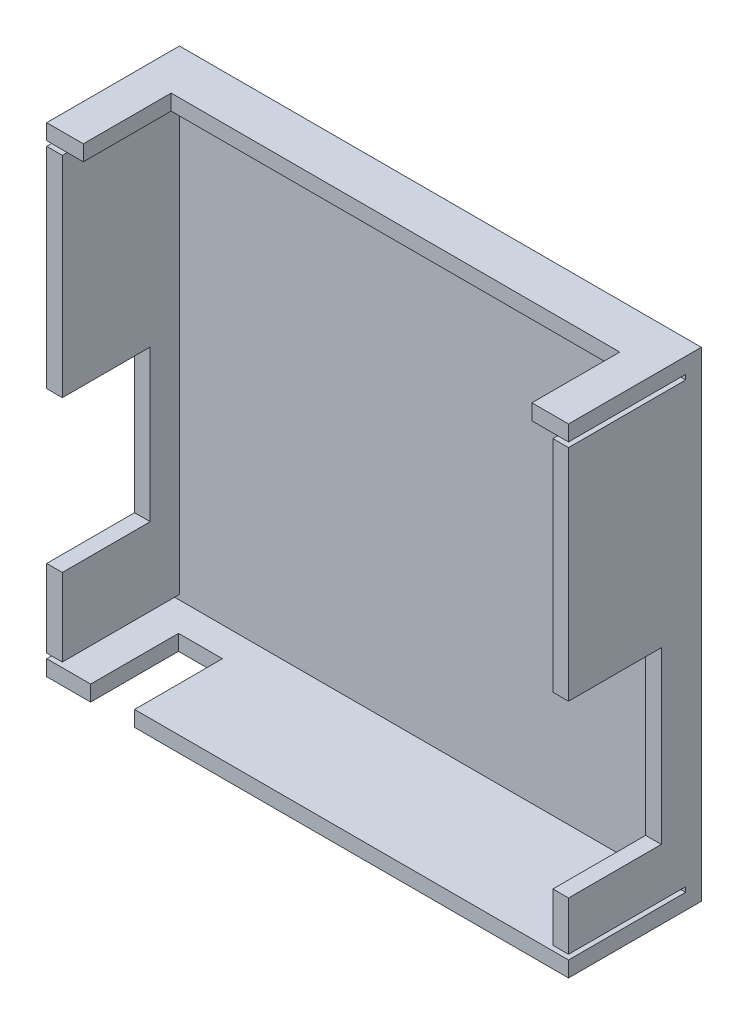
SolidWorks part; units mm, degrees
ref_plane "Front Plane" through (0, 0, 0) normal (0, 0, 1) x (1, 0, 0)
ref_plane "Top Plane" through (0, 0, 0) normal (0, 1, 0) x (1, 0, 0)
ref_plane "Right Plane" through (0, 0, 0) normal (1, 0, 0) x (0, 0, -1)
sketch "Sketch1" plane through (0, 0, 0) normal (0, 0, 1) x (1, 0, 0)
  line L1 (0, 0) -> (106.9, 0)
  line L2 (0, 0) -> (0, 98.3)
  line L3 (0, 98.3) -> (106.9, 98.3)
  line L4 (106.9, 0) -> (106.9, 98.3)
  dimension "D1" = 98.3
  dimension "D2" = 106.9
extrude "Boss-Extrude2" add sketch "Sketch1" along normal blind 3.2
sketch "Sketch2" plane through (0, 0, 3.2) normal (0, 0, 1) x (1, 0, 0)
  line L1 (3.2, 3.2) -> (103.7, 3.2)
  line L2 (3.2, 3.2) -> (3.2, 95.1)
  line L3 (3.2, 95.1) -> (103.7, 95.1)
  line L4 (0, 98.3) -> (0, 0)
  line L5 (0, 0) -> (106.9, 0)
  line L6 (106.9, 0) -> (106.9, 98.3)
  line L7 (106.9, 98.3) -> (0, 98.3)
  line L8 (0, 98.3) -> (0, 0)
  line L9 (0, 0) -> (106.9, 0)
  line L10 (106.9, 0) -> (106.9, 98.3)
  line L11 (106.9, 98.3) -> (0, 98.3)
  line L12 (103.7, 3.2) -> (103.7, 95.1)
  dimension "D2" = 3.2
  dimension "D3" = 3.2
  dimension "D4" = 3.2
  dimension "D5" = 3.2
  dimension "D1" = 0
extrude "Boss-Extrude3" add sketch "Sketch2" along normal blind 24
sketch "Sketch3" plane through (0, 0, 27.2) normal (0, 0, 1) x (1, 0, 0)
  line L0 (3.2, 95.1) -> (0, 95.1)
  line L1 (0, 95.1) -> (0, 94.1)
  line L2 (0, 94.1) -> (3.2, 94.1)
  line L3 (3.2, 95.1) -> (3.2, 3.2) construction
  line L4 (106.9, 98.3) -> (0, 98.3)
  line L5 (0, 98.3) -> (0, 0)
  line L6 (0, 0) -> (106.9, 0)
  line L7 (106.9, 0) -> (106.9, 98.3)
  line L9 (0, 95.1) -> (0, 94.1)
  line L11 (106.9, 3.2) -> (106.9, 4.2)
  line L12 (3.2, 94.1) -> (3.2, 95.1)
  line L13 (103.7, 95.1) -> (106.9, 95.1)
  line L14 (106.9, 95.1) -> (106.9, 94.1)
  line L15 (106.9, 94.1) -> (103.7, 94.1)
  line L16 (103.7, 3.2) -> (103.7, 95.1) construction
  line L17 (103.7, 94.1) -> (103.7, 95.1)
  line L18 (103.7, 3.2) -> (106.9, 3.2)
  line L19 (106.9, 3.2) -> (106.9, 4.2)
  line L20 (106.9, 4.2) -> (103.7, 4.2)
  line L21 (103.7, 4.2) -> (103.7, 3.2)
  line L22 (3.2, 3.2) -> (0, 3.2)
  line L23 (0, 3.2) -> (0, 4.2)
  line L24 (0, 4.2) -> (3.2, 4.2)
  line L25 (3.2, 4.2) -> (3.2, 3.2)
  line L26 (0, 4.2) -> (0, 0)
  line L27 (106.9, 94.1) -> (106.9, 95.1)
  line M10 (0, 98.3) -> (0, 0)
  line M12 (106.9, 0) -> (106.9, 98.3)
  line M14 (3.2, 3.2) -> (3.2, 95.1)
  line M16 (103.7, 95.1) -> (103.7, 3.2)
  dimension "D1" = 0
  dimension "D2" = 1
  dimension "D3" = 1
  dimension "D4" = 1
  dimension "D5" = 1
extrude "Cut-Extrude1" cut sketch "Sketch3" against normal blind 24 contours L2 L0 M10 M14 | L15 L13 M12 M16 | L20 L18 M12 M16 | L24 L25 L22 L23
sketch "Sketch4" plane through (0, 0, 27.2) normal (0, 0, 1) x (1, 0, 0)
  line L0 (0, 51.1) -> (3.2, 51.1)
  line L1 (0, 20.1) -> (3.2, 20.1)
  line L4 (0, 94.1) -> (0, 4.2)
  line L5 (0, 4.2) -> (3.2, 4.2)
  line L6 (3.2, 4.2) -> (3.2, 94.1)
  line L7 (3.2, 94.1) -> (0, 94.1)
  line L8 (0, 51.1) -> (0, 20.1)
  line L9 (0, 4.2) -> (3.2, 4.2) construction
  line L10 (3.2, 20.1) -> (3.2, 51.1)
  line L11 (3.2, 94.1) -> (0, 94.1) construction
  dimension "D2" = 43
  dimension "D3" = 31
  dimension "D1" = 0
extrude "Cut-Extrude2" cut sketch "Sketch4" against normal blind 18
sketch "Sketch5" plane through (0, 0, 27.2) normal (0, 0, 1) x (1, 0, 0)
  line L4 (0, 95.1) -> (106.9, 95.1)
  line L5 (106.9, 95.1) -> (106.9, 98.3)
  line L6 (106.9, 98.3) -> (0, 98.3)
  line L7 (0, 98.3) -> (0, 95.1)
  line L9 (106.9, 95.1) -> (106.9, 98.3) construction
  line L11 (0, 98.3) -> (0, 95.1) construction
  line L14 (7.5, 98.3) -> (7.5, 95.1)
  line L15 (106.9, 98.3) -> (0, 98.3) construction
  line L16 (106.9, 95.1) -> (0, 95.1) construction
  line L17 (7.5, 95.1) -> (99.4, 95.1)
  line L18 (99.4, 95.1) -> (99.4, 98.3)
  line L19 (99.4, 98.3) -> (7.5, 98.3)
  point P10 (106.9, 96.7)
  dimension "D2" = 7.5
  dimension "D3" = 7.5
  dimension "D1" = 0
extrude "Cut-Extrude3" cut sketch "Sketch5" against normal blind 18
sketch "Sketch6" plane through (0, 0, 27.2) normal (0, 0, 1) x (1, 0, 0)
  line L0 (103.7, 14.2) -> (106.9, 14.2)
  line L1 (103.7, 49.1) -> (106.9, 49.1)
  line L4 (103.7, 4.2) -> (106.9, 4.2)
  line L5 (106.9, 4.2) -> (106.9, 94.1)
  line L6 (106.9, 94.1) -> (103.7, 94.1)
  line L7 (103.7, 94.1) -> (103.7, 4.2)
  line L8 (103.7, 4.2) -> (106.9, 4.2) construction
  line L9 (106.9, 14.2) -> (106.9, 49.1)
  line L10 (106.9, 94.1) -> (103.7, 94.1) construction
  line L11 (103.7, 49.1) -> (103.7, 14.2)
  point P8 (105.3, 4.2)
  dimension "D2" = 45
  dimension "D3" = 10
  dimension "D1" = 0
extrude "Cut-Extrude4" cut sketch "Sketch6" against normal blind 19
sketch "Sketch7" plane through (0, 0, 27.2) normal (0, 0, 1) x (1, 0, 0)
  line L0 (9, 3.2) -> (9, 0)
  line L1 (18, 3.2) -> (18, 0)
  line L4 (106.9, 3.2) -> (0, 3.2)
  line L5 (0, 3.2) -> (0, 0)
  line L6 (0, 0) -> (106.9, 0)
  line L7 (106.9, 0) -> (106.9, 3.2)
  line L8 (18, 3.2) -> (9, 3.2)
  line L9 (0, 3.2) -> (0, 0) construction
  line L10 (9, 0) -> (18, 0)
  line L11 (106.9, 0) -> (106.9, 3.2) construction
  dimension "D2" = 9
  dimension "D3" = 9
  dimension "D1" = 0
extrude "Cut-Extrude5" cut sketch "Sketch7" against normal blind 18
equation "\"WallThickness\"= 3.2mm"
equation "\"D2@Sketch2\"=\"WallThickness\""
equation "\"D3@Sketch2\"=\"WallThickness\""
equation "\"D4@Sketch2\"=\"WallThickness\""
equation "\"D5@Sketch2\"=\"WallThickness\""
equation "\"CornerBreakDist\"= 1mm"
equation "\"D2@Sketch3\"=\"CornerBreakDist\""
equation "\"D3@Sketch3\"=\"CornerBreakDist\""
equation "\"D4@Sketch3\"=\"CornerBreakDist\""
equation "\"D5@Sketch3\"=\"CornerBreakDist\""
